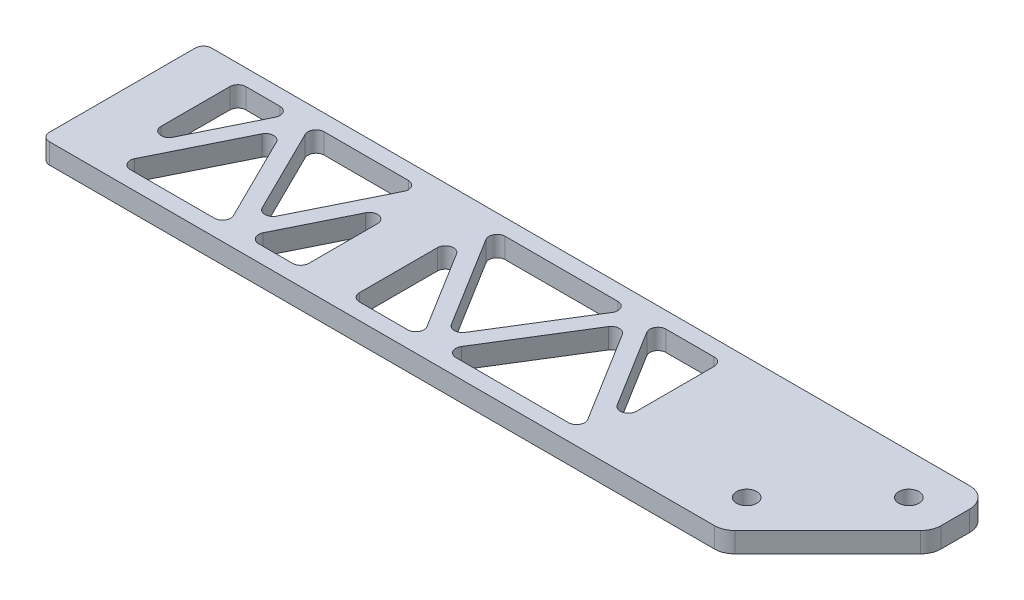
SolidWorks part; units mm, degrees
ref_plane "Front Plane" through (0, 0, 0) normal (0, 0, 1) x (1, 0, 0)
ref_plane "Top Plane" through (0, 0, 0) normal (0, 1, 0) x (1, 0, 0)
ref_plane "Right Plane" through (0, 0, 0) normal (1, 0, 0) x (0, 0, -1)
sketch "Sketch1" plane through (0, 0, 0) normal (0, 1, 0) x (1, 0, 0)
  line L0 (121.4655, -25.4) -> (172.2655, 25.4)
  line L1 (-92.075, 25.4) -> (172.2655, 25.4)
  line L2 (-92.075, 25.4) -> (-92.075, -25.4)
  line L3 (-92.075, -25.4) -> (121.4655, -25.4)
  line L5 (81.915, 25.4) -> (81.915, -25.4)
  line L6 (-76.2, 20.32) -> (-15.875, 20.32)
  line L7 (-76.2, 20.32) -> (-76.2, -20.32)
  line L8 (-76.2, -20.32) -> (-15.875, -20.32)
  line L9 (-15.875, 20.32) -> (-15.875, -20.32)
  line L10 (0, 20.32) -> (75.565, 20.32)
  line L11 (0, 20.32) -> (0, -20.32)
  line L12 (0, -20.32) -> (75.565, -20.32)
  line L13 (75.565, 20.32) -> (75.565, -20.32)
  line L14 (-76.2, -20.32) -> (-56.0917, 20.32)
  line L15 (-56.0917, 20.32) -> (-35.9833, -20.32)
  line L16 (-35.9833, -20.32) -> (-15.875, 20.32)
  line L17 (116.205, -12.7) -> (141.605, 12.7) construction
  line L18 (0, 20.32) -> (25.1883, -20.32)
  line L19 (25.1883, -20.32) -> (50.3767, 20.32)
  line L20 (50.3767, 20.32) -> (75.565, -20.32)
  line L21 (-73.9234, -21.4464) -> (-56.0917, 14.5925)
  line L22 (-56.0917, 14.5925) -> (-35.9833, -26.0475)
  line L23 (-35.9833, -26.0475) -> (-13.5984, 19.1936)
  line L24 (-2.159, 18.9819) -> (25.1883, -25.1415)
  line L25 (25.1883, -25.1415) -> (50.3767, 15.4985)
  line L26 (50.3767, 15.4985) -> (73.406, -21.6581)
  line L27 (-78.4766, -19.1936) -> (-56.0917, 26.0475)
  line L28 (-56.0917, 26.0475) -> (-35.9833, -14.5925)
  line L29 (-35.9833, -14.5925) -> (-18.1516, 21.4464)
  line L30 (2.159, 21.6581) -> (25.1883, -15.4985)
  line L31 (25.1883, -15.4985) -> (50.3767, 25.1415)
  line L32 (50.3767, 25.1415) -> (77.724, -18.9819)
  line L33 (154.305, 7.4395) -> (154.305, 25.4)
  circle A0 centre (141.605, 12.7) radius 3.175
  circle A1 centre (116.205, -12.7) radius 3.175
  point P6 (0, 0)
  point P19 (-15.875, 0)
  point P42 (-92.075, 0)
  dimension "D5" = 6.35
  dimension "D9" = 6.35
  dimension "D2" = 76.2
  dimension "D3" = 15.875
  dimension "D4" = 5.08
  dimension "D6" = 75.565
  dimension "D7" = 15.875
  dimension "D8" = 50.8
  dimension "D10" = 25.4
  dimension "D11" = 2.54
  dimension "D13" = 12.7
  dimension "D14" = 81.915
  dimension "D15" = 34.29
  dimension "D16" = 12.7
  dimension "D17" = 12.7
  dimension "D18" = 12.7
  dimension "D12" = 2.54
extrude "Boss-Extrude1" add sketch "Sketch1" along normal mid plane 6.35
fillet "Fillet1" radius 2.54 26 edges at (-92.075, 0, -25.4) (-92.075, 0, 25.4) (2.9883, 0, -20.32) (25.1883, 0, 15.4985) (47.3884, 0, -20.32) (0, 0, -15.4985) (0, 0, 20.32) (22.2, 0, 20.32) (72.5767, 0, 20.32) (50.3767, 0, -15.4985) (28.1766, 0, 20.32) (75.565, 0, 15.4985) (75.565, 0, -20.32) (53.365, 0, -20.32) (-76.2, 0, -20.32) (-76.2, 0, 14.5925) (-58.9256, 0, -20.32) (-73.3661, 0, 20.32) (-38.8172, 0, 20.32) (-15.875, 0, 20.32) (-15.875, 0, -14.5925) (-33.1494, 0, 20.32) (-35.9833, 0, 14.5925) (-18.7089, 0, -20.32) (-53.2578, 0, -20.32) (-56.0917, 0, -14.5925)
fillet "Fillet2" radius 6.35 3 edges at (154.305, 0, -25.4) (154.305, 0, -7.4395) (121.4655, 0, 25.4)
